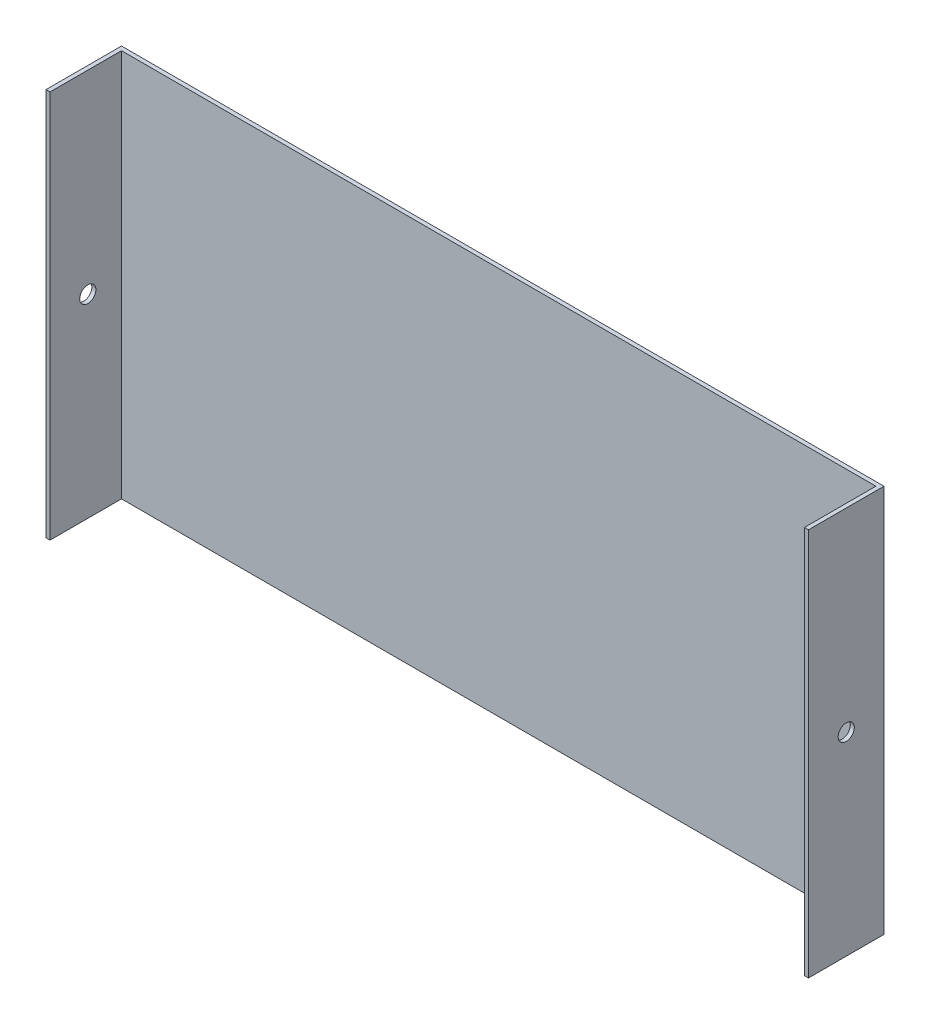
SolidWorks part; units mm, degrees
ref_plane "Front Plane" through (0, 0, 0) normal (0, 0, 1) x (1, 0, 0)
ref_plane "Top Plane" through (0, 0, 0) normal (0, 1, 0) x (1, 0, 0)
ref_plane "Right Plane" through (0, 0, 0) normal (1, 0, 0) x (0, 0, -1)
sketch "Sketch1" plane through (0, 0, 0) normal (0, 1, 0) x (1, 0, 0)
  line L0 (299.3406, 54.0892) -> (299.3406, 50.9142) construction
  line L1 (3.175, 2.0975) -> (595.5063, 2.0975)
  line L2 (0, 0) -> (0, -53.975)
  line L3 (0, -53.975) -> (3.175, -53.975)
  line L4 (3.175, 2.0975) -> (3.175, -53.975)
  line L5 (598.6813, 0) -> (598.6813, 5.2725)
  line L6 (598.6813, 5.2725) -> (0, 5.2725)
  line L7 (595.5063, 2.0975) -> (595.5063, -53.975)
  line L8 (598.6813, -53.975) -> (595.5063, -53.975)
  line L9 (0, 5.2725) -> (0, 0)
  line L11 (598.6813, 0) -> (598.6813, -53.975)
  dimension "D1" = 3.175
extrude "Boss-Extrude1" add sketch "Sketch1" along normal blind 304.8
sketch "Sketch2" plane through (0, 0, 0) normal (-1, 0, 0) x (0, 0, 1)
  line L0 (-5.2725, 152.4) -> (53.975, 152.4) construction
  line L1 (-5.2725, 304.8) -> (-5.2725, 0) construction
  line L2 (53.975, 304.8) -> (53.975, 0) construction
  circle A0 centre (24.3512, 152.4) radius 6.35
extrude "Cut-Extrude1" cut sketch "Sketch2" against normal through all
